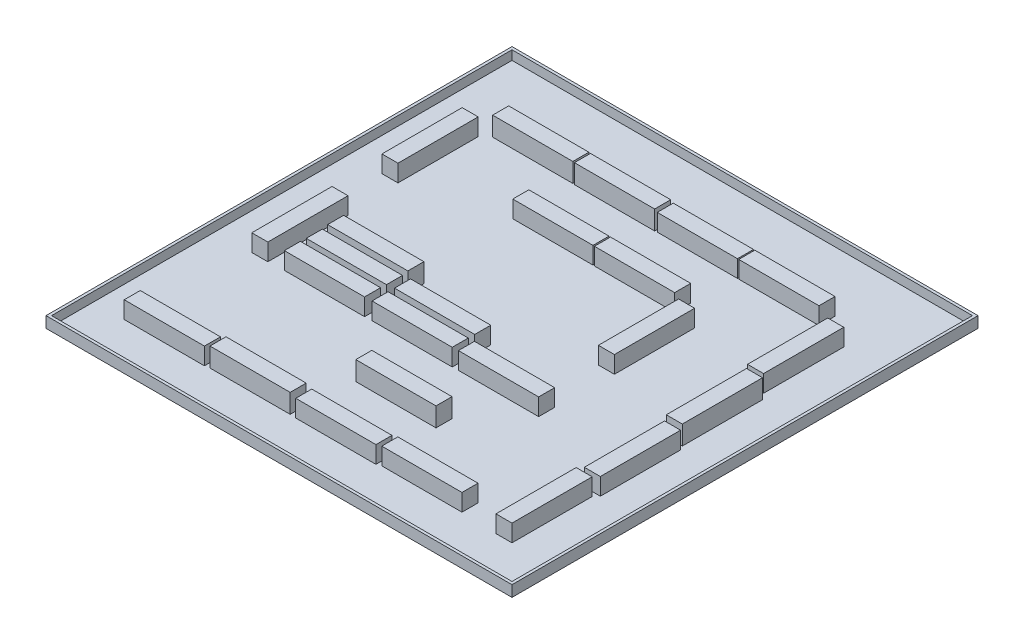
SolidWorks part; units mm, degrees
other "Kamera1"
ref_plane "Ön Düzlem" through (0, 0, 0) normal (0, 0, 1) x (1, 0, 0)
ref_plane "Üst Düzlem" through (0, 0, 0) normal (0, 1, 0) x (1, 0, 0)
ref_plane "Sağ Düzlem" through (0, 0, 0) normal (1, 0, 0) x (0, 0, -1)
sketch "Çizim2" plane through (0, 0, 0) normal (0, 1, 0) x (1, 0, 0)
  line L1 (-2530, 2530) -> (2530, 2530)
  line L2 (-2530, 2530) -> (-2530, -2530)
  line L3 (-2530, -2530) -> (2530, -2530)
  line L4 (2530, 2530) -> (2530, -2530)
  line L5 (-2530, 2530) -> (2530, -2530) construction
  line L6 (-2530, -2530) -> (2530, 2530) construction
  point P0 (0, 0)
  dimension "D1" = 5060
  dimension "D2" = 5060
extrude "Yükseklik-Ekstrüzyon1" add sketch "Çizim2" along normal blind 20
sketch "Çizim3" plane through (0, 20, 0) normal (0, 1, 0) x (1, 0, 0)
  line L1 (-2500, -2500) -> (2500, -2500)
  line L2 (-2500, -2500) -> (-2500, 2500)
  line L3 (-2500, 2500) -> (2500, 2500)
  line L4 (2500, -2500) -> (2500, 2500)
  line L5 (-2500, -2500) -> (2500, 2500) construction
  line L6 (-2500, 2500) -> (2500, -2500) construction
  line L7 (2530, -2530) -> (-2530, -2530)
  line L8 (2530, -2530) -> (2530, 2530)
  line L9 (2530, 2530) -> (-2530, 2530)
  line L10 (-2530, -2530) -> (-2530, 2530)
  line L11 (2530, -2530) -> (-2530, 2530) construction
  line L12 (2530, 2530) -> (-2530, -2530) construction
  point P0 (0, 0)
  point P5 (0, 0)
extrude "Yükseklik-Ekstrüzyon2" add sketch "Çizim3" along normal blind 100
sketch "Çizim4" plane through (0, 20, 0) normal (0, 1, 0) x (1, 0, 0)
  line L1 (-1883.4579, 1847.1939) -> (-1012.4579, 1847.1939)
  line L2 (-1883.4579, 1847.1939) -> (-1883.4579, 1673.1939)
  line L3 (-1883.4579, 1673.1939) -> (-1012.4579, 1673.1939)
  line L4 (-1012.4579, 1847.1939) -> (-1012.4579, 1673.1939)
  line L5 (-1883.4579, 1847.1939) -> (-1012.4579, 1673.1939) construction
  line L6 (-1883.4579, 1673.1939) -> (-1012.4579, 1847.1939) construction
  point P0 (-1447.9579, 1760.1939)
  dimension "D1" = 871
  dimension "D2" = 174
sketch "Çizim5" plane through (0, 20, 0) normal (0, 1, 0) x (1, 0, 0)
  line L1 (-992.4625, 1844.3026) -> (-121.4625, 1844.3026)
  line L2 (-992.4625, 1844.3026) -> (-992.4625, 1670.3026)
  line L3 (-992.4625, 1670.3026) -> (-121.4625, 1670.3026)
  line L4 (-121.4625, 1844.3026) -> (-121.4625, 1670.3026)
  line L5 (-992.4625, 1844.3026) -> (-121.4625, 1670.3026) construction
  line L6 (-992.4625, 1670.3026) -> (-121.4625, 1844.3026) construction
  point P0 (-556.9625, 1757.3026)
  dimension "D1" = 871
  dimension "D2" = 174
sketch "Çizim6" plane through (0, 20, 0) normal (0, 1, 0) x (1, 0, 0)
  line L1 (-96.4529, 1847.8491) -> (774.5471, 1847.8491)
  line L2 (-96.4529, 1847.8491) -> (-96.4529, 1673.8491)
  line L3 (-96.4529, 1673.8491) -> (774.5471, 1673.8491)
  line L4 (774.5471, 1847.8491) -> (774.5471, 1673.8491)
  line L5 (-96.4529, 1847.8491) -> (774.5471, 1673.8491) construction
  line L6 (-96.4529, 1673.8491) -> (774.5471, 1847.8491) construction
  point P0 (339.0471, 1760.8491)
  dimension "D1" = 871
  dimension "D2" = 174
sketch "Çizim7" plane through (0, 20, 0) normal (0, 1, 0) x (1, 0, 0)
  line L1 (-1006.4032, 1188.8355) -> (-135.4032, 1188.8355)
  line L2 (-1006.4032, 1188.8355) -> (-1006.4032, 1014.8355)
  line L3 (-1006.4032, 1014.8355) -> (-135.4032, 1014.8355)
  line L4 (-135.4032, 1188.8355) -> (-135.4032, 1014.8355)
  line L5 (-1006.4032, 1188.8355) -> (-135.4032, 1014.8355) construction
  line L6 (-1006.4032, 1014.8355) -> (-135.4032, 1188.8355) construction
  point P0 (-570.9032, 1101.8355)
  dimension "D1" = 871
  dimension "D2" = 174
sketch "Çizim8" plane through (0, 20, 0) normal (0, 1, 0) x (1, 0, 0)
  line L1 (-118.6233, 1187.922) -> (752.3767, 1187.922)
  line L2 (-118.6233, 1187.922) -> (-118.6233, 1013.922)
  line L3 (-118.6233, 1013.922) -> (752.3767, 1013.922)
  line L4 (752.3767, 1187.922) -> (752.3767, 1013.922)
  line L5 (-118.6233, 1187.922) -> (752.3767, 1013.922) construction
  line L6 (-118.6233, 1013.922) -> (752.3767, 1187.922) construction
  point P0 (316.8767, 1100.922)
  dimension "D1" = 871
  dimension "D2" = 174
sketch "Çizim9" plane through (0, 20, 0) normal (0, 1, 0) x (1, 0, 0)
  line L1 (-810.695, -291.05) -> (60.305, -291.05)
  line L2 (-810.695, -291.05) -> (-810.695, -465.05)
  line L3 (-810.695, -465.05) -> (60.305, -465.05)
  line L4 (60.305, -291.05) -> (60.305, -465.05)
  line L5 (-810.695, -291.05) -> (60.305, -465.05) construction
  line L6 (-810.695, -465.05) -> (60.305, -291.05) construction
  point P0 (-375.195, -378.05)
  dimension "D1" = 871
  dimension "D2" = 174
sketch "Çizim10" plane through (0, 20, 0) normal (0, 1, 0) x (1, 0, 0)
  line L1 (-1749.9686, -77.9266) -> (-878.9686, -77.9266)
  line L2 (-1749.9686, -77.9266) -> (-1749.9686, -251.9266)
  line L3 (-1749.9686, -251.9266) -> (-878.9686, -251.9266)
  line L4 (-878.9686, -77.9266) -> (-878.9686, -251.9266)
  line L5 (-1749.9686, -77.9266) -> (-878.9686, -251.9266) construction
  line L6 (-1749.9686, -251.9266) -> (-878.9686, -77.9266) construction
  point P0 (-1314.4686, -164.9266)
  dimension "D1" = 871
  dimension "D2" = 174
sketch "Çizim11" plane through (0, 20, 0) normal (0, 1, 0) x (1, 0, 0)
  line L1 (605.8323, -1845.9694) -> (1476.8323, -1845.9694)
  line L2 (605.8323, -1845.9694) -> (605.8323, -2019.9694)
  line L3 (605.8323, -2019.9694) -> (1476.8323, -2019.9694)
  line L4 (1476.8323, -1845.9694) -> (1476.8323, -2019.9694)
  line L5 (605.8323, -1845.9694) -> (1476.8323, -2019.9694) construction
  line L6 (605.8323, -2019.9694) -> (1476.8323, -1845.9694) construction
  point P0 (1041.3323, -1932.9694)
  dimension "D1" = 871
  dimension "D2" = 174
sketch "Çizim12" plane through (0, 20, 0) normal (0, 1, 0) x (1, 0, 0)
  line L1 (788.3588, 1847.9163) -> (1659.3588, 1847.9163)
  line L2 (788.3588, 1847.9163) -> (788.3588, 1673.9163)
  line L3 (788.3588, 1673.9163) -> (1659.3588, 1673.9163)
  line L4 (1659.3588, 1847.9163) -> (1659.3588, 1673.9163)
  line L5 (788.3588, 1847.9163) -> (1659.3588, 1673.9163) construction
  line L6 (788.3588, 1673.9163) -> (1659.3588, 1847.9163) construction
  point P0 (1223.8588, 1760.9163)
  dimension "D1" = 871
  dimension "D2" = 174
sketch "Çizim13" plane through (0, 20, 0) normal (0, 1, 0) x (1, 0, 0)
  line L1 (1822.2116, 735.3051) -> (1822.2116, 1606.3051)
  line L2 (1822.2116, 735.3051) -> (1996.2116, 735.3051)
  line L3 (1996.2116, 735.3051) -> (1996.2116, 1606.3051)
  line L4 (1822.2116, 1606.3051) -> (1996.2116, 1606.3051)
  line L5 (1822.2116, 735.3051) -> (1996.2116, 1606.3051) construction
  line L6 (1996.2116, 735.3051) -> (1822.2116, 1606.3051) construction
  point P0 (1909.2116, 1170.8051)
  dimension "D1" = 871
  dimension "D2" = 174
sketch "Çizim17" plane through (0, 20, 0) normal (0, 1, 0) x (1, 0, 0)
  line L1 (1877.1305, -201.8214) -> (1877.1305, 669.1786)
  line L2 (1877.1305, -201.8214) -> (2051.1305, -201.8214)
  line L3 (2051.1305, -201.8214) -> (2051.1305, 669.1786)
  line L4 (1877.1305, 669.1786) -> (2051.1305, 669.1786)
  line L5 (1877.1305, -201.8214) -> (2051.1305, 669.1786) construction
  line L6 (2051.1305, -201.8214) -> (1877.1305, 669.1786) construction
  point P0 (1964.1305, 233.6786)
  dimension "D1" = 871
  dimension "D2" = 174
sketch "Çizim18" plane through (0, 20, 0) normal (0, 1, 0) x (1, 0, 0)
  line L1 (1904.2335, -1118.7374) -> (1904.2335, -247.7374)
  line L2 (1904.2335, -1118.7374) -> (2078.2335, -1118.7374)
  line L3 (2078.2335, -1118.7374) -> (2078.2335, -247.7374)
  line L4 (1904.2335, -247.7374) -> (2078.2335, -247.7374)
  line L5 (1904.2335, -1118.7374) -> (2078.2335, -247.7374) construction
  line L6 (2078.2335, -1118.7374) -> (1904.2335, -247.7374) construction
  point P0 (1991.2335, -683.2374)
  dimension "D1" = 871
  dimension "D2" = 174
sketch "Çizim19" plane through (0, 20, 0) normal (0, 1, 0) x (1, 0, 0)
  line L1 (-2140.8447, 728.6434) -> (-2140.8447, 1599.6434)
  line L2 (-2140.8447, 728.6434) -> (-1966.8447, 728.6434)
  line L3 (-1966.8447, 728.6434) -> (-1966.8447, 1599.6434)
  line L4 (-2140.8447, 1599.6434) -> (-1966.8447, 1599.6434)
  line L5 (-2140.8447, 728.6434) -> (-1966.8447, 1599.6434) construction
  line L6 (-1966.8447, 728.6434) -> (-2140.8447, 1599.6434) construction
  point P0 (-2053.8447, 1164.1434)
  dimension "D1" = 871
  dimension "D2" = 174
sketch "Çizim20" plane through (0, 20, 0) normal (0, 1, 0) x (1, 0, 0)
  line L1 (833.725, 104.2695) -> (833.725, 975.2695)
  line L2 (833.725, 104.2695) -> (1007.725, 104.2695)
  line L3 (1007.725, 104.2695) -> (1007.725, 975.2695)
  line L4 (833.725, 975.2695) -> (1007.725, 975.2695)
  line L5 (833.725, 104.2695) -> (1007.725, 975.2695) construction
  line L6 (1007.725, 104.2695) -> (833.725, 975.2695) construction
  point P0 (920.725, 539.7695)
  dimension "D1" = 871
  dimension "D2" = 174
sketch "Çizim21" plane through (0, 20, 0) normal (0, 1, 0) x (1, 0, 0)
  line L1 (1862.5491, -2036.8466) -> (1862.5491, -1165.8466)
  line L2 (1862.5491, -2036.8466) -> (2036.5491, -2036.8466)
  line L3 (2036.5491, -2036.8466) -> (2036.5491, -1165.8466)
  line L4 (1862.5491, -1165.8466) -> (2036.5491, -1165.8466)
  line L5 (1862.5491, -2036.8466) -> (2036.5491, -1165.8466) construction
  line L6 (2036.5491, -2036.8466) -> (1862.5491, -1165.8466) construction
  point P0 (1949.5491, -1601.3466)
  dimension "D1" = 871
  dimension "D2" = 174
sketch "Çizim22" plane through (0, 20, 0) normal (0, 1, 0) x (1, 0, 0)
  line L1 (-812.0576, -533.8429) -> (58.9424, -533.8429)
  line L2 (-812.0576, -533.8429) -> (-812.0576, -707.8429)
  line L3 (-812.0576, -707.8429) -> (58.9424, -707.8429)
  line L4 (58.9424, -533.8429) -> (58.9424, -707.8429)
  line L5 (-812.0576, -533.8429) -> (58.9424, -707.8429) construction
  line L6 (-812.0576, -707.8429) -> (58.9424, -533.8429) construction
  point P0 (-376.5576, -620.8429)
  dimension "D1" = 871
  dimension "D2" = 174
sketch "Çizim23" plane through (0, 20, 0) normal (0, 1, 0) x (1, 0, 0)
  line L1 (-1761.5241, -536.5165) -> (-890.5241, -536.5165)
  line L2 (-1761.5241, -536.5165) -> (-1761.5241, -710.5165)
  line L3 (-1761.5241, -710.5165) -> (-890.5241, -710.5165)
  line L4 (-890.5241, -536.5165) -> (-890.5241, -710.5165)
  line L5 (-1761.5241, -536.5165) -> (-890.5241, -710.5165) construction
  line L6 (-1761.5241, -710.5165) -> (-890.5241, -536.5165) construction
  point P0 (-1326.0241, -623.5165)
  dimension "D1" = 871
  dimension "D2" = 174
sketch "Çizim24" plane through (0, 20, 0) normal (0, 1, 0) x (1, 0, 0)
  line L1 (-1758.057, -301.9365) -> (-887.057, -301.9365)
  line L2 (-1758.057, -301.9365) -> (-1758.057, -475.9365)
  line L3 (-1758.057, -475.9365) -> (-887.057, -475.9365)
  line L4 (-887.057, -301.9365) -> (-887.057, -475.9365)
  line L5 (-1758.057, -301.9365) -> (-887.057, -475.9365) construction
  line L6 (-1758.057, -475.9365) -> (-887.057, -301.9365) construction
  point P0 (-1322.557, -388.9365)
  dimension "D1" = 871
  dimension "D2" = 174
sketch "Çizim25" plane through (0, 20, 0) normal (0, 1, 0) x (1, 0, 0)
  line L1 (-327.6914, -1194.5126) -> (543.3086, -1194.5126)
  line L2 (-327.6914, -1194.5126) -> (-327.6914, -1368.5126)
  line L3 (-327.6914, -1368.5126) -> (543.3086, -1368.5126)
  line L4 (543.3086, -1194.5126) -> (543.3086, -1368.5126)
  line L5 (-327.6914, -1194.5126) -> (543.3086, -1368.5126) construction
  line L6 (-327.6914, -1368.5126) -> (543.3086, -1194.5126) construction
  point P0 (107.8086, -1281.5126)
  dimension "D1" = 871
  dimension "D2" = 174
sketch "Çizim26" plane through (0, 20, 0) normal (0, 1, 0) x (1, 0, 0)
  line L1 (123.6515, -531.408) -> (994.6515, -531.408)
  line L2 (123.6515, -531.408) -> (123.6515, -705.408)
  line L3 (123.6515, -705.408) -> (994.6515, -705.408)
  line L4 (994.6515, -531.408) -> (994.6515, -705.408)
  line L5 (123.6515, -531.408) -> (994.6515, -705.408) construction
  line L6 (123.6515, -705.408) -> (994.6515, -531.408) construction
  point P0 (559.1515, -618.408)
  dimension "D1" = 871
  dimension "D2" = 174
sketch "Çizim27" plane through (0, 20, 0) normal (0, 1, 0) x (1, 0, 0)
  line L1 (-311.0795, -1863.2955) -> (559.9205, -1863.2955)
  line L2 (-311.0795, -1863.2955) -> (-311.0795, -2037.2955)
  line L3 (-311.0795, -2037.2955) -> (559.9205, -2037.2955)
  line L4 (559.9205, -1863.2955) -> (559.9205, -2037.2955)
  line L5 (-311.0795, -1863.2955) -> (559.9205, -2037.2955) construction
  line L6 (-311.0795, -2037.2955) -> (559.9205, -1863.2955) construction
  point P0 (124.4205, -1950.2955)
  dimension "D1" = 871
  dimension "D2" = 174
sketch "Çizim28" plane through (0, 20, 0) normal (0, 1, 0) x (1, 0, 0)
  line L1 (-1246.8889, -1858.8345) -> (-375.8889, -1858.8345)
  line L2 (-1246.8889, -1858.8345) -> (-1246.8889, -2032.8345)
  line L3 (-1246.8889, -2032.8345) -> (-375.8889, -2032.8345)
  line L4 (-375.8889, -1858.8345) -> (-375.8889, -2032.8345)
  line L5 (-1246.8889, -1858.8345) -> (-375.8889, -2032.8345) construction
  line L6 (-1246.8889, -2032.8345) -> (-375.8889, -1858.8345) construction
  point P0 (-811.3889, -1945.8345)
  dimension "D1" = 871
  dimension "D2" = 174
sketch "Çizim29" plane through (0, 20, 0) normal (0, 1, 0) x (1, 0, 0)
  line L1 (-2168.7402, -1867.9267) -> (-1297.7402, -1867.9267)
  line L2 (-2168.7402, -1867.9267) -> (-2168.7402, -2041.9267)
  line L3 (-2168.7402, -2041.9267) -> (-1297.7402, -2041.9267)
  line L4 (-1297.7402, -1867.9267) -> (-1297.7402, -2041.9267)
  line L5 (-2168.7402, -1867.9267) -> (-1297.7402, -2041.9267) construction
  line L6 (-2168.7402, -2041.9267) -> (-1297.7402, -1867.9267) construction
  point P0 (-1733.2402, -1954.9267)
  dimension "D1" = 871
  dimension "D2" = 174
sketch "Çizim30" plane through (0, 20, 0) normal (0, 1, 0) x (1, 0, 0)
  line L1 (-2106.0154, -719.257) -> (-2106.0154, 151.743)
  line L2 (-2106.0154, -719.257) -> (-1932.0154, -719.257)
  line L3 (-1932.0154, -719.257) -> (-1932.0154, 151.743)
  line L4 (-2106.0154, 151.743) -> (-1932.0154, 151.743)
  line L5 (-2106.0154, -719.257) -> (-1932.0154, 151.743) construction
  line L6 (-1932.0154, -719.257) -> (-2106.0154, 151.743) construction
  point P0 (-2019.0154, -283.757)
  dimension "D1" = 871
  dimension "D2" = 174
extrude "Yükseklik-Ekstrüzyon3" add sketch "Çizim4" along normal blind 207
extrude "Yükseklik-Ekstrüzyon4" add sketch "Çizim5" along normal blind 207
extrude "Yükseklik-Ekstrüzyon5" add sketch "Çizim6" along normal blind 185.7
extrude "Yükseklik-Ekstrüzyon6" add sketch "Çizim7" along normal blind 185.7
extrude "Yükseklik-Ekstrüzyon7" add sketch "Çizim8" along normal blind 185.7
extrude "Yükseklik-Ekstrüzyon8" add sketch "Çizim9" along normal blind 185.7
extrude "Yükseklik-Ekstrüzyon9" add sketch "Çizim10" along normal blind 207
extrude "Yükseklik-Ekstrüzyon10" add sketch "Çizim11" along normal blind 185.7
extrude "Yükseklik-Ekstrüzyon11" add sketch "Çizim12" along normal blind 185.7
extrude "Yükseklik-Ekstrüzyon12" add sketch "Çizim18" along normal blind 185.7
extrude "Yükseklik-Ekstrüzyon13" add sketch "Çizim13" along normal blind 185.7
extrude "Yükseklik-Ekstrüzyon14" add sketch "Çizim17" along normal blind 207
extrude "Yükseklik-Ekstrüzyon15" add sketch "Çizim19" along normal blind 185.7
extrude "Yükseklik-Ekstrüzyon16" add sketch "Çizim20" along normal blind 185.7
extrude "Yükseklik-Ekstrüzyon17" add sketch "Çizim21" along normal blind 185.7
extrude "Yükseklik-Ekstrüzyon18" add sketch "Çizim22" along normal blind 185.7
extrude "Yükseklik-Ekstrüzyon19" add sketch "Çizim23" along normal blind 185.7
extrude "Yükseklik-Ekstrüzyon20" add sketch "Çizim24" along normal blind 185.7
extrude "Yükseklik-Ekstrüzyon21" add sketch "Çizim25" along normal blind 207
extrude "Yükseklik-Ekstrüzyon22" add sketch "Çizim26" along normal blind 185.7
extrude "Yükseklik-Ekstrüzyon23" add sketch "Çizim28" along normal blind 207
extrude "Yükseklik-Ekstrüzyon24" add sketch "Çizim27" along normal blind 185.7
extrude "Yükseklik-Ekstrüzyon25" add sketch "Çizim29" along normal blind 185.7
extrude "Yükseklik-Ekstrüzyon26" add sketch "Çizim30" along normal blind 185.7
sketch "Çizim31" plane through (0, 20, 0) normal (0, 1, 0) x (1, 0, 0)
  line L0 (1665.169, -2563.5674) -> (762.0742, -1743.3115)
  line L1 (1665.169, -2563.5674) -> (2485.4249, -1660.4726)
  line L2 (762.0742, -1743.3115) -> (1582.3301, -840.2167)
  line L3 (2485.4249, -1660.4726) -> (1582.3301, -840.2167)
  line L4 (1665.169, -2563.5674) -> (1582.3301, -840.2167) construction
  line L5 (762.0742, -1743.3115) -> (2485.4249, -1660.4726) construction
  point P0 (1623.7496, -1701.892)
  point P1 (1623.7496, -1701.892)
